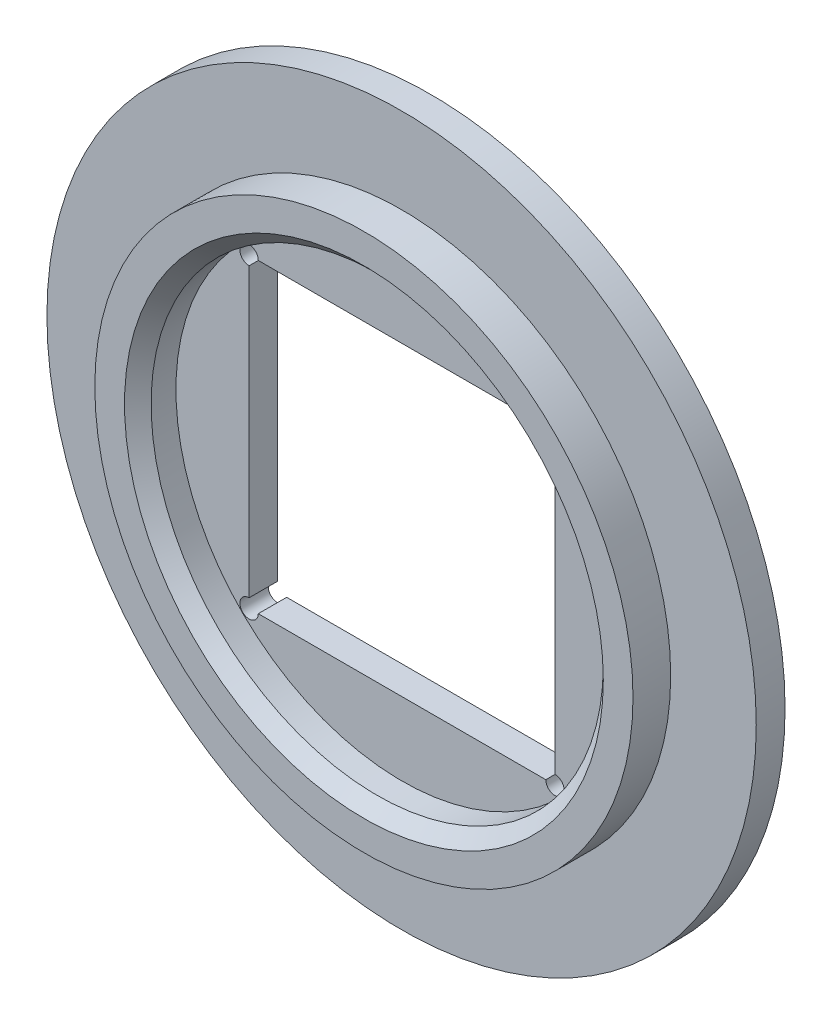
SolidWorks part; units mm, degrees
ref_plane "前视基准面" through (0, 0, 0) normal (0, 0, 1) x (1, 0, 0)
ref_plane "上视基准面" through (0, 0, 0) normal (0, 1, 0) x (1, 0, 0)
ref_plane "右视基准面" through (0, 0, 0) normal (1, 0, 0) x (0, 0, -1)
sketch "草图1" plane through (0, 0, 0) normal (0, 0, 1) x (1, 0, 0)
  circle A0 centre (0, 0) radius 8
extrude "凸台-拉伸1" add sketch "草图1" along normal blind 0.65
sketch "草图2" plane through (0, 0, 0) normal (0, 0, 1) x (1, 0, 0)
  circle A0 centre (0, 0) radius 6.07
  circle A1 centre (0, 0) radius 5.1
extrude "凸台-拉伸2" add sketch "草图2" along normal blind 0.85 from surface at 0.65 starting at face at (8, 0, 0.65)
sketch "草图3" plane through (0, 0, 0) normal (0, 0, 1) x (1, 0, 0)
  circle A0 centre (0, 0) radius 5.1
extrude "切除-拉伸1" cut sketch "草图3" against normal blind 0.01 from surface at 0.65 starting at face at (6.07, 0, 0.65)
sketch "草图4" plane through (0, 0, 0) normal (0, 0, 1) x (1, 0, 0)
  line L21 (-3.45, 3.45) -> (3.45, 3.45)
  line L24 (-3.45, 3.45) -> (-3.45, -3.45)
  line L25 (-3.45, -3.45) -> (3.45, -3.45)
  line L26 (3.45, -3.45) -> (3.45, 3.45)
extrude "切除-拉伸2" cut sketch "草图4" along normal up to surface (0.64 mm away) up to face at (5.1, 0, 0.64)
chamfer "倒角1" distance 0.3 angle 45 1 edges at (5.1, 0, 1.5)
sketch "草图6" plane through (0, 0, 0) normal (0, 0, 1) x (1, 0, 0)
  circle A1 centre (-3.45, 3.45) radius 0.2074
  circle A2 centre (3.45, 3.45) radius 0.2074
  circle A3 centre (3.45, -3.45) radius 0.2074
  circle A4 centre (-3.45, -3.45) radius 0.2074
extrude "切除-拉伸3" cut sketch "草图6" along normal up to surface (0.64 mm away) from surface at 0 up to face at (0, 0, 0.64) starting at face at (8, 0, 0)
